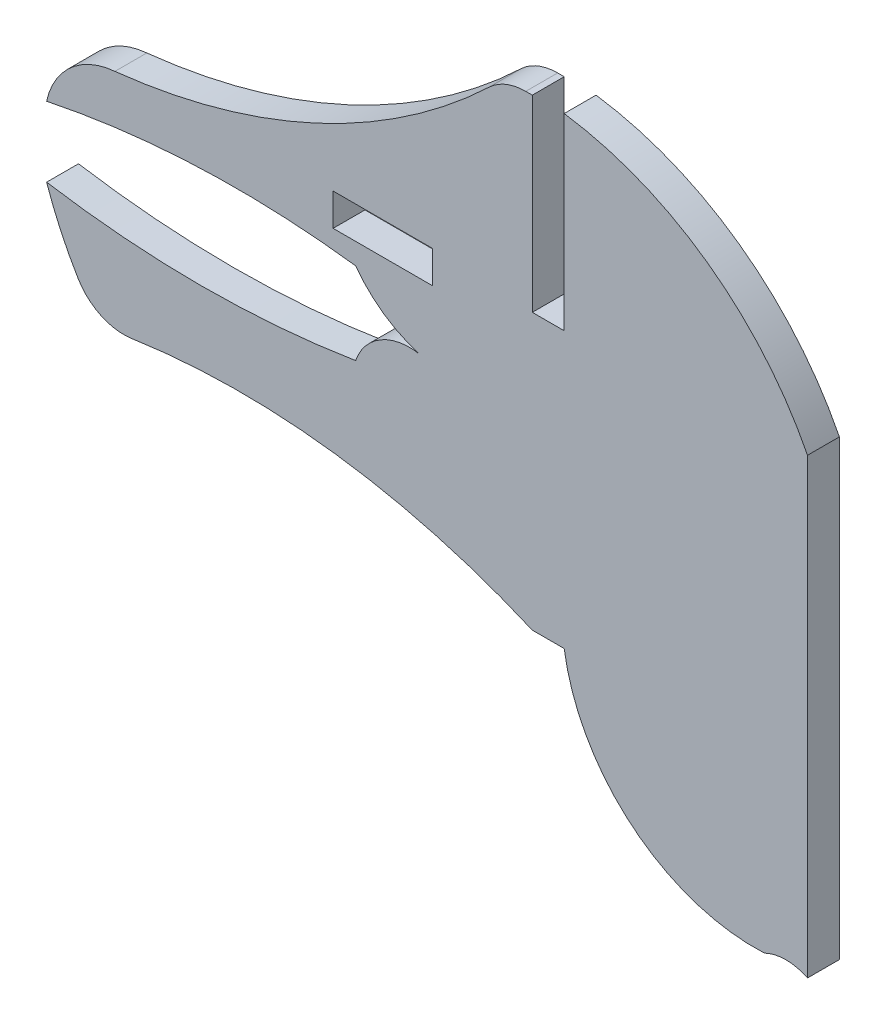
SolidWorks part; units mm, degrees
ref_plane "Front Plane" through (0, 0, 0) normal (0, 0, 1) x (1, 0, 0)
ref_plane "Top Plane" through (0, 0, 0) normal (0, 1, 0) x (1, 0, 0)
ref_plane "Right Plane" through (0, 0, 0) normal (1, 0, 0) x (0, 0, -1)
sketch "Sketch1" plane through (0, 0, 0) normal (0, 0, 1) x (1, 0, 0)
  line L0 (0, 15.4404) -> (-1.524, 15.4404)
  line L1 (-1.524, 15.4404) -> (-1.524, 24.4352)
  line L2 (-1.524, 24.4352) -> (-1.8368, 24.4352)
  line L3 (-1.524, 2.2811) -> (0, 2.2811)
  line L4 (0, 15.4404) -> (0, 24.4352)
  line L5 (11.6339, 16.1008) -> (11.6339, -5.5442)
  line L7 (-11.049, 15.7019) -> (-6.2865, 15.7019)
  line L8 (-11.049, 15.7019) -> (-11.049, 14.1562)
  line L9 (-11.049, 14.1562) -> (-6.2865, 14.1562)
  line L10 (-6.2865, 15.7019) -> (-6.2865, 14.1562)
  arc A0 (-3.5892, 23.7338) -> (-21.4807, 15.4404) centre (-24.7472, 45.9328) cw
  arc A1 (-1.8368, 24.4352) -> (-3.5892, 23.7338) centre (-1.8368, 21.8952) ccw
  arc A2 (-21.4807, 15.4404) -> (-24.7472, 12.5692) centre (-21.1725, 11.796) ccw
  arc A3 (-24.7472, 12.5692) -> (-9.9728, 13.1429) centre (-15.651, -31.1557) cw
  arc A4 (-9.9728, 13.1429) -> (-6.9059, 11.0137) centre (-5.3515, 16.526) ccw
  arc A5 (-6.9059, 11.0137) -> (-9.9728, 9.2191) centre (-7.3881, 8.3199) ccw
  arc A6 (-9.9728, 9.2191) -> (-24.7472, 9.2191) centre (-17.36, 54.9065) cw
  arc A7 (-24.7472, 9.2191) -> (-23.2416, 5.9832) centre (-8.6274, 14.7512) ccw
  arc A8 (-20.6893, 4.7777) -> (-1.524, 2.2811) centre (-15.4904, -30.1226) cw
  arc A9 (-23.2416, 5.9832) -> (-20.6893, 4.7777) centre (-21.0635, 7.29) ccw
  arc A10 (0, 24.4352) -> (11.6339, 16.1008) centre (-2.1775, 9.1086) cw
  arc A11 (0, 2.2811) -> (9.5738, -5.5442) centre (9.1245, 3.6753) ccw
  arc A12 (11.6339, -5.5442) -> (9.5738, -5.5442) centre (10.6039, -7.6529) ccw
  dimension "D1" = 2.54
  dimension "D2" = 2.54
  dimension "D3" = 4.7625
  dimension "D4" = 4.7625
extrude "Boss-Extrude1" add sketch "Sketch1" along normal blind 1.524
